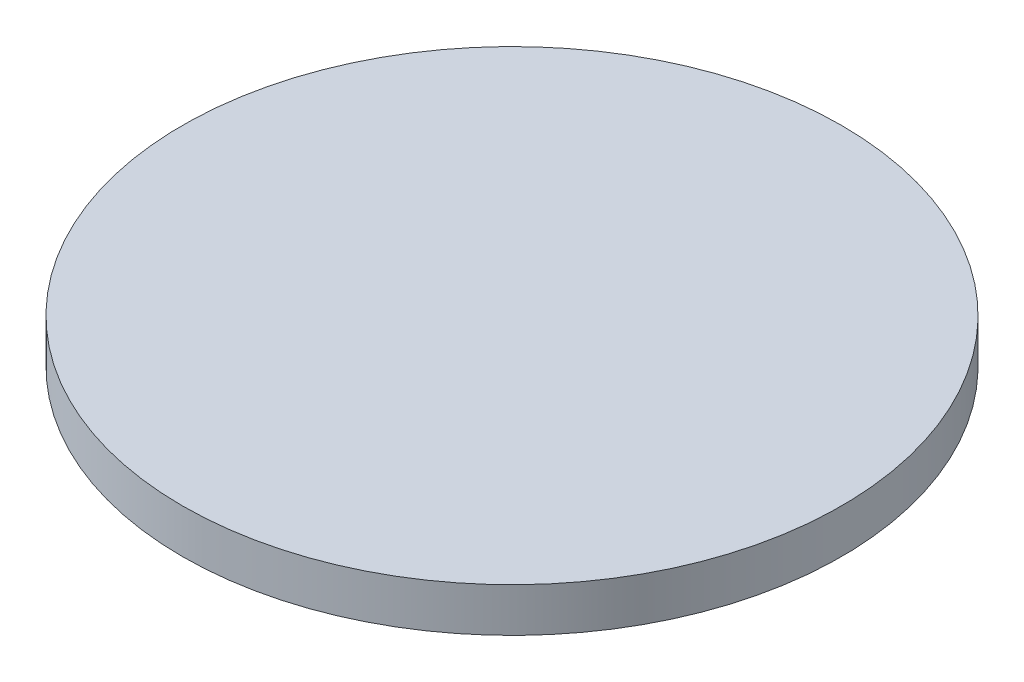
SolidWorks part; units mm, degrees
ref_plane "Front Plane" through (0, 0, 0) normal (0, 0, 1) x (1, 0, 0)
ref_plane "Top Plane" through (0, 0, 0) normal (0, 1, 0) x (1, 0, 0)
ref_plane "Right Plane" through (0, 0, 0) normal (1, 0, 0) x (0, 0, -1)
sketch "Sketch1" plane through (0, 0, 0) normal (0, 0, 1) x (1, 0, 0)
  line L0 (0, 3.9) -> (-15, 3.9)
  line L1 (-15, 3.9) -> (-15, 1.9)
  line L2 (-15, 1.9) -> (-4.96, 1.9)
  line L3 (-4.96, 1.9) -> (-4.96, 0)
  line L4 (-4.96, 0) -> (0, 0)
  line L5 (0, 3.9) -> (0, 0) construction
  line L6 (0, 3.9) -> (0, 0)
  dimension "D1" = 15
  dimension "D2" = 2
  dimension "D3" = 1.9
  dimension "D4" = 4.96
revolve "Revolve1" add sketch "Sketch1" angle 360 about L5
sketch "Sketch2" plane through (0, 0, 0) normal (0, -1, 0) x (1, 0, 0)
  circle A0 centre (0, 0) radius 2.81
  dimension "D1" = 5.62
extrude "Cut-Extrude1" cut sketch "Sketch2" against normal blind 3.03
